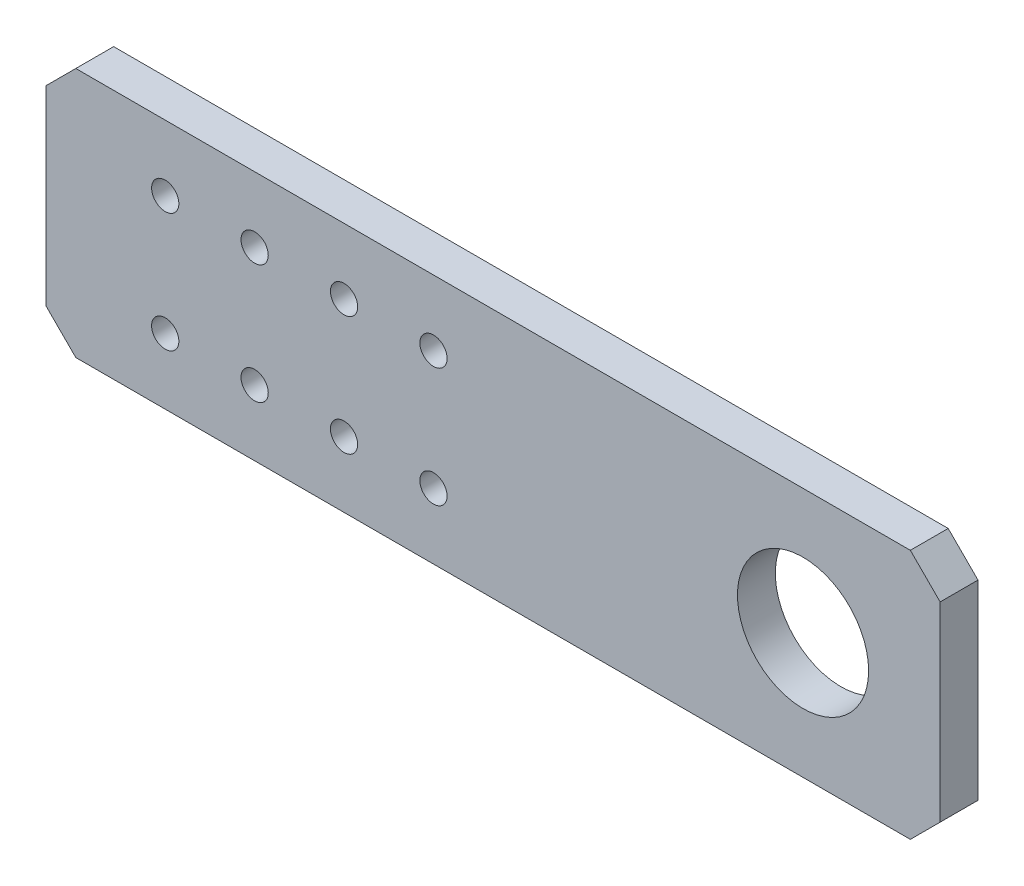
SolidWorks part; units mm, degrees
ref_plane "Front Plane" through (0, 0, 0) normal (0, 0, 1) x (1, 0, 0)
ref_plane "Top Plane" through (0, 0, 0) normal (0, 1, 0) x (1, 0, 0)
ref_plane "Right Plane" through (0, 0, 0) normal (1, 0, 0) x (0, 0, -1)
sketch "Sketch1" plane through (0, 0, 0) normal (0, 0, 1) x (1, 0, 0)
  line L1 (-102.5, 21) -> (102.5, 21)
  line L2 (-102.5, 21) -> (-102.5, -21)
  line L3 (-102.5, -21) -> (102.5, -21)
  line L4 (102.5, 21) -> (102.5, -21)
  line L5 (-102.5, 21) -> (102.5, -21) construction
  line L6 (-102.5, -21) -> (102.5, 21) construction
  point P0 (0, 0)
  dimension "D1" = 205
  dimension "D2" = 42
extrude "Boss-Extrude1" add sketch "Sketch1" along normal blind 6.35
sketch "Sketch3" plane through (0, 0, 6.35) normal (0, 0, 1) x (1, 0, 0)
  line L0 (-62.5, 10) -> (-62.5, -10) construction
  line L1 (-102.5, 21) -> (-102.5, -21) construction
  circle A0 centre (-62.5, 10) radius 2
  circle A1 centre (-62.5, -10) radius 2
  point P4 (-62.5, 0)
  dimension "D1" = 4
  dimension "D2" = 20
  dimension "D3" = 40
sketch "Sketch4" plane through (0, 0, 6.35) normal (0, 0, 1) x (1, 0, 0)
  line L0 (-102.5, 21) -> (-102.5, -21) construction
  line L1 (102.5, -21) -> (102.5, 21) construction
  circle A0 centre (-78.5, 0) radius 11
  circle A1 centre (82.5, 0) radius 11 construction
  dimension "D2" = 22
  dimension "D3" = 20
  dimension "D1" = 24
  dimension "D4" = 161
extrude "Cut-Extrude3" cut sketch "Sketch4" against normal through all
chamfer "Chamfer1" distance 5 angle 45 4 edges at (-102.5, 21, 3.175) (-102.5, -21, 3.175) (102.5, 21, 3.175) (102.5, -21, 3.175)
sketch "Sketch5" plane through (0, 0, 6.35) normal (0, 0, 1) x (1, 0, 0)
  line L0 (102.5, -16) -> (102.5, 16) construction
  circle A0 centre (79.5, 0) radius 11
  dimension "D1" = 22
  dimension "D2" = 23
extrude "Cut-Extrude4" cut sketch "Sketch5" against normal blind 25
sketch "Sketch7" plane through (0, 0, 6.35) normal (0, 0, 1) x (1, 0, 0)
  line L4 (7.5, 3.175) -> (-7.5, 3.175)
  line L5 (7.5, -3.175) -> (7.5, 3.175)
  line L6 (-7.5, -3.175) -> (7.5, -3.175)
  line L7 (-7.5, 3.175) -> (-7.5, -3.175)
  line L8 (7.5, 3.175) -> (-7.5, 3.175)
  line L9 (7.5, -3.175) -> (7.5, 3.175)
  line L10 (-7.5, -3.175) -> (7.5, -3.175)
  line L11 (-7.5, 3.175) -> (-7.5, -3.175)
  dimension "D1" = 0
sketch "Sketch8" [suppressed] plane through (0, 0, 6.35) normal (0, 0, 1) x (1, 0, 0)
  line L4 (25.5, 3.175) -> (10.5, 3.175)
  line L5 (10.5, 3.175) -> (10.5, -3.175)
  line L6 (10.5, -3.175) -> (25.5, -3.175)
  line L7 (25.5, -3.175) -> (25.5, 3.175)
  line L8 (25.5, 3.175) -> (10.5, 3.175)
  line L9 (10.5, 3.175) -> (10.5, -3.175)
  line L10 (10.5, -3.175) -> (25.5, -3.175)
  line L11 (25.5, -3.175) -> (25.5, 3.175)
  dimension "D1" = 0
extrude "Cut-Extrude7" [suppressed] cut sketch "Sketch8" against normal through all
sketch "Sketch9" [suppressed] plane through (0, 0, 6.35) normal (0, 0, 1) x (1, 0, 0)
  circle A0 centre (80, 0) radius 11 construction
  circle A1 centre (80, 0) radius 11
extrude "Cut-Extrude8" [suppressed] cut sketch "Sketch9" against normal through all
sketch "Sketch10" [suppressed] plane through (0, 0, 6.35) normal (0, 0, 1) x (1, 0, 0)
  circle A0 centre (80, 0) radius 15
  dimension "D1" = 25
extrude "Cut-Extrude9" [suppressed] cut sketch "Sketch10" against normal through all
sketch "Sketch11" [suppressed] plane through (0, 0, 6.35) normal (0, 0, 1) x (1, 0, 0)
  circle A0 centre (95.5563, 15.5563) radius 1.5 construction
  circle A1 centre (64.4437, 15.5563) radius 1.5 construction
  circle A2 centre (95.5563, -15.5563) radius 1.5 construction
  circle A3 centre (64.4437, -15.5563) radius 1.5 construction
  circle A4 centre (95.5563, 15.5563) radius 1.5
  circle A5 centre (64.4437, 15.5563) radius 1.5
  circle A6 centre (95.5563, -15.5563) radius 1.5
  circle A7 centre (64.4437, -15.5563) radius 1.5
extrude "Cut-Extrude10" [suppressed] cut sketch "Sketch11" against normal through all
sketch "Sketch12" [suppressed] plane through (0, 0, 6.35) normal (0, 0, 1) x (1, 0, 0)
  line L0 (-100, 16) -> (-100, -16) construction
  circle A0 centre (-93, 0) radius 3.302
  point P4 (-100, 0)
  dimension "D1" = 6.604
  dimension "D2" = 7
extrude "Cut-Extrude11" [suppressed] cut sketch "Sketch12" against normal through all
sketch "Sketch13" plane through (0, 0, 6.35) normal (0, 0, 1) x (1, 0, 0)
  line L0 (-47.5, 16) -> (-47.5, -16)
  line L1 (-42.5, 21) -> (-47.5, 16)
  line L2 (-47.5, -16) -> (-42.5, -21)
  line L3 (97.5, 21) -> (-97.5, 21) construction
  line L4 (-97.5, 21) -> (-102.5, 16) construction
  line L5 (-102.5, 16) -> (-102.5, -16) construction
  line L6 (-102.5, -16) -> (-97.5, -21) construction
  line L7 (-97.5, -21) -> (97.5, -21) construction
  line L8 (97.5, 21) -> (-97.5, 21)
  line L9 (-97.5, 21) -> (-102.5, 16)
  line L10 (-102.5, 16) -> (-102.5, -16)
  line L11 (-102.5, -16) -> (-97.5, -21)
  line L12 (-97.5, -21) -> (97.5, -21)
  line L13 (97.5, -21) -> (102.5, -16)
  line L14 (102.5, -16) -> (102.5, 16)
  line L15 (102.5, 16) -> (97.5, 21)
  line L16 (97.5, 21) -> (-42.5, 21)
  line L20 (-42.5, -21) -> (97.5, -21)
  line L21 (97.5, -21) -> (102.5, -16)
  line L22 (102.5, -16) -> (102.5, 16)
  line L23 (102.5, 16) -> (97.5, 21)
  line L24 (97.5, 21) -> (-97.5, 21)
  line L25 (-97.5, 21) -> (-102.5, 16)
  line L26 (-102.5, 16) -> (-102.5, -16)
  line L27 (-102.5, -16) -> (-97.5, -21)
  line L28 (-97.5, -21) -> (97.5, -21)
  line L29 (-47.5, 0) -> (16.1615, 0) construction
  line L30 (-27.5, 10) -> (-12.5, 10) construction
  circle A0 centre (-27.5, 10) radius 2.286
  circle A1 centre (-12.5, 10) radius 2.286
  circle A2 centre (-12.5, -10) radius 2.286
  circle A3 centre (-27.5, -10) radius 2.286
  circle A4 centre (2.5, 10) radius 2.286
  circle A5 centre (17.5, 10) radius 2.286
  circle A6 centre (17.5, -10) radius 2.286
  circle A7 centre (2.5, -10) radius 2.286
  point P2 (-47.5, 21)
  point P9 (-47.5, -21)
  circle M20 centre (-78.5, 0) radius 11
  line M21 (97.5, 21) -> (-97.5, 21)
  line M22 (-97.5, 21) -> (-102.5, 16)
  line M23 (-102.5, 16) -> (-102.5, -16)
  line M24 (-102.5, -16) -> (-97.5, -21)
  line M25 (-97.5, -21) -> (97.5, -21)
  dimension "D4" = 4.572
  dimension "D2" = 150
  dimension "D3" = 15
  dimension "D7" = 10
  dimension "D8" = 20
  dimension "D1" = 0
  dimension "D9" = 2
extrude "Cut-Extrude12" cut sketch "Sketch13" against normal blind 10 contours L2 L0 L1 M21 M22 M23 M24 M25 M20 | A0 | A1 | A2 | A3 | A4 | A5 | A6 | A7
